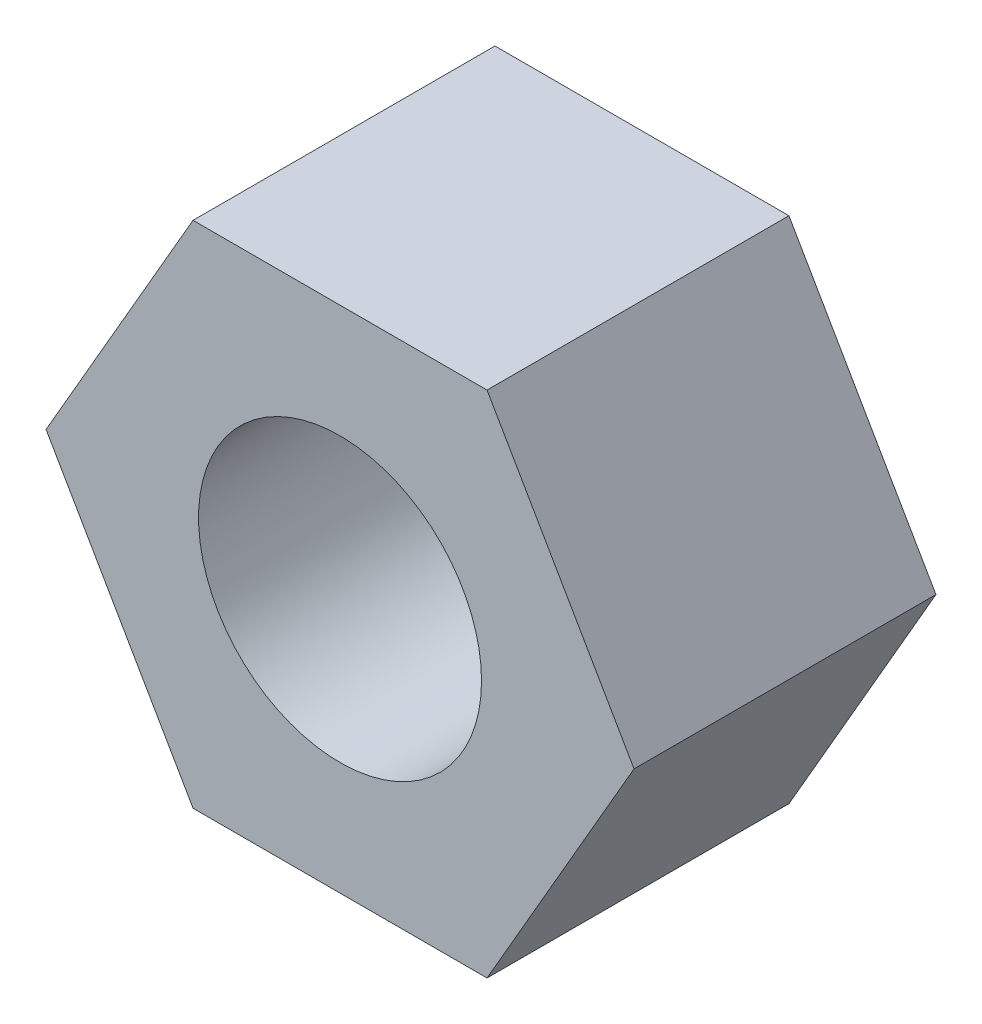
SolidWorks part; units mm, degrees
ref_plane "Front Plane" through (0, 0, 0) normal (0, 0, 1) x (1, 0, 0)
ref_plane "Top Plane" through (0, 0, 0) normal (0, 1, 0) x (1, 0, 0)
ref_plane "Right Plane" through (0, 0, 0) normal (1, 0, 0) x (0, 0, -1)
sketch "Sketch1" plane through (0, 0, 0) normal (0, 0, 1) x (1, 0, 0)
  line L1 (8.2856, 0) -> (4.1428, 7.1755)
  line L2 (4.1428, 7.1755) -> (-4.1428, 7.1755)
  line L3 (-4.1428, 7.1755) -> (-8.2856, 0)
  line L4 (-8.2856, 0) -> (-4.1428, -7.1755)
  line L5 (-4.1428, -7.1755) -> (4.1428, -7.1755)
  line L6 (4.1428, -7.1755) -> (8.2856, 0)
  circle A0 centre (0, 0) radius 7.1755 construction
  circle A1 centre (0, 0) radius 3.9878
  dimension "D2" = 7.9756
  dimension "D1" = 14.351
extrude "Boss-Extrude1" add sketch "Sketch1" along normal blind 8.509
